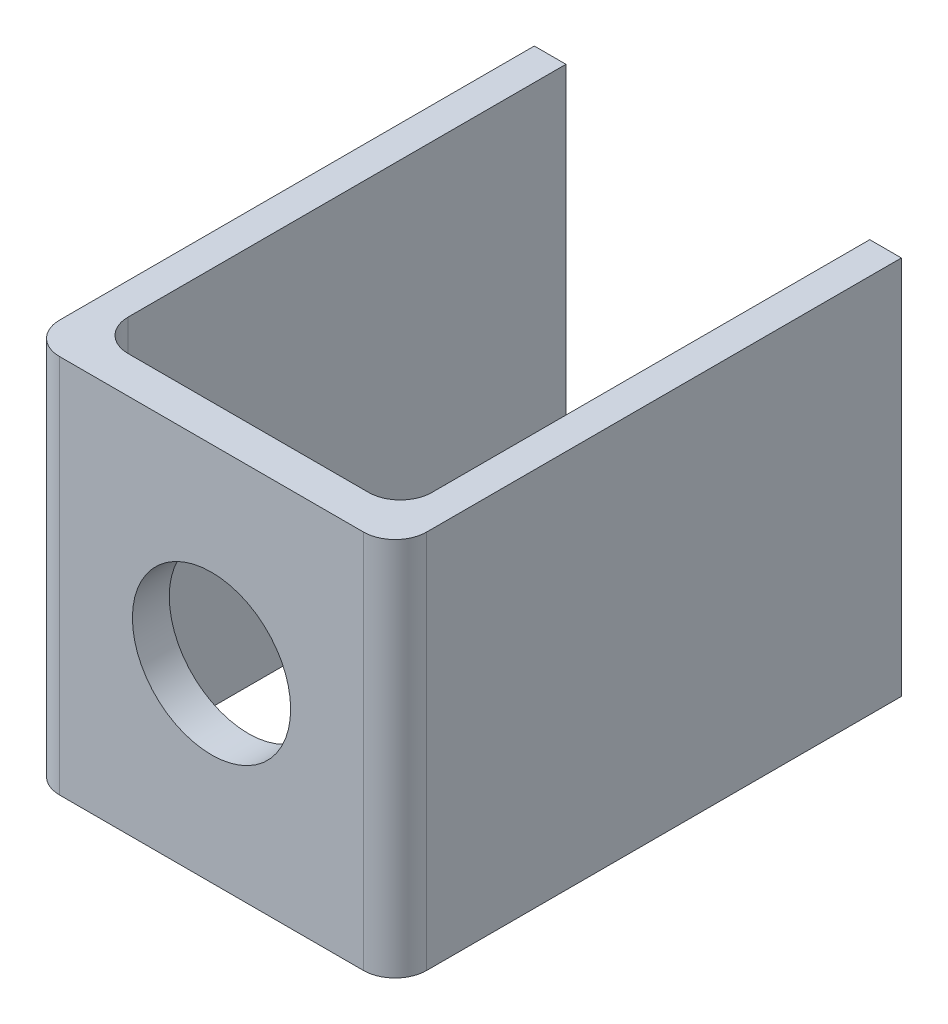
SolidWorks part; units mm, degrees
ref_plane "Спереди" through (0, 0, 0) normal (0, 0, 1) x (1, 0, 0)
ref_plane "Сверху" through (0, 0, 0) normal (0, 1, 0) x (1, 0, 0)
ref_plane "Справа" through (0, 0, 0) normal (1, 0, 0) x (0, 0, -1)
sketch "Эскиз1" plane through (0, 0, 0) normal (0, 1, 0) x (1, 0, 0)
  line L0 (0, 80) -> (0, 5)
  line L1 (5, 0) -> (53, 0)
  line L2 (58, 5) -> (58, 80)
  line L3 (0, 80) -> (5, 80)
  line L4 (5, 80) -> (5, 10.8222)
  line L5 (10, 5.8222) -> (48, 5.8222)
  line L6 (53, 10.8222) -> (53, 80)
  line L7 (53, 80) -> (58, 80)
  arc A0 (5, 10.8222) -> (10, 5.8222) centre (10, 10.8222) ccw
  arc A1 (48, 5.8222) -> (53, 10.8222) centre (48, 10.8222) ccw
  arc A2 (53, 0) -> (58, 5) centre (53, 5) ccw
  arc A3 (0, 5) -> (5, 0) centre (5, 5) ccw
  point P17 (0, 0)
  dimension "D1" = 5
extrude "Бобышка-Вытянуть1" add sketch "Эскиз1" along normal blind 60
sketch "Эскиз2" plane through (0, 0, 0) normal (0, 0, 1) x (1, 0, 0)
  circle A0 centre (29, 30) radius 12.5
extrude "Вырез-Вытянуть1" cut sketch "Эскиз2" against normal through all
